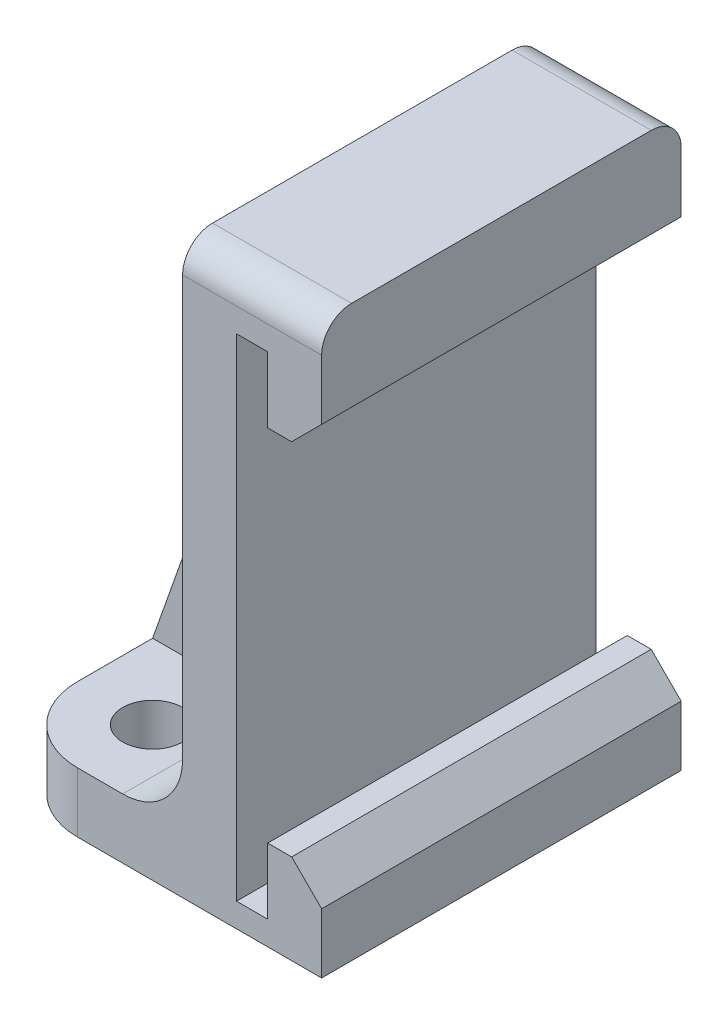
SolidWorks part; units mm, degrees
ref_plane "Front Plane" through (0, 0, 0) normal (0, 0, 1) x (1, 0, 0)
ref_plane "Top Plane" through (0, 0, 0) normal (0, 1, 0) x (1, 0, 0)
ref_plane "Right Plane" through (0, 0, 0) normal (1, 0, 0) x (0, 0, -1)
sketch "Sketch1" plane through (0, 0, 0) normal (0, 0, 1) x (1, 0, 0)
  line L0 (0, 0) -> (0, 25.4) construction
  line L1 (0, 25.4) -> (1.016, 25.4) construction
  line L2 (1.016, 25.4) -> (1.016, 0) construction
  line L3 (1.016, 0) -> (0, 0) construction
  line L4 (-0.3175, -0.3175) -> (-0.3175, 25.7175)
  line L5 (-0.3175, 25.7175) -> (1.3335, 25.7175)
  line L6 (1.3335, 25.7175) -> (1.3335, -0.3175) construction
  line L7 (1.3335, -0.3175) -> (-0.3175, -0.3175)
  line L8 (0.7937, 0) -> (0.7938, -1.5875) construction
  line L9 (1.016, 0) -> (4.191, 0) construction
  line L10 (4.191, -1.5875) -> (4.191, 0)
  line L11 (4.191, 0) -> (4.191, 3.175)
  line L12 (4.191, 3.175) -> (1.3335, 3.175)
  line L13 (1.016, 25.4) -> (1.016, 28.575) construction
  line L14 (1.016, 28.575) -> (4.191, 28.575)
  line L15 (4.191, 28.575) -> (4.191, 22.225)
  line L16 (4.191, 22.225) -> (1.3335, 22.225)
  line L17 (1.016, 28.575) -> (-3.175, 28.575)
  line L18 (-3.175, 28.575) -> (-3.175, -0.3175) construction
  line L20 (-3.175, -1.5875) -> (4.191, -1.5875)
  line L21 (-3.175, -1.5875) -> (-12.7, -1.5875)
  line L22 (-12.7, -1.5875) -> (-12.7, 1.5875)
  line L23 (-12.7, 1.5875) -> (-3.175, 1.5875)
  line L24 (1.3335, 25.7175) -> (1.3335, 22.225)
  line L25 (1.3335, 3.175) -> (1.3335, -0.3175)
  line L26 (-3.175, 28.575) -> (-3.175, 1.5875)
extrude "Boss-Extrude1" add sketch "Sketch1" along normal mid plane 19.05
fillet "Fillet1" radius 3.175 1 edges at (-3.175, 1.5875, 0)
sketch "Sketch2" plane through (0, 0, 0) normal (0, 0, 1) x (1, 0, 0)
  line L0 (-3.175, 28.575) -> (-12.7, 1.5875)
  line L1 (-12.7, 1.5875) -> (-3.175, 1.5875)
  line L2 (-3.175, 1.5875) -> (-3.175, 28.575)
extrude "Boss-Extrude2" add sketch "Sketch2" along normal mid plane 3.175
sketch "Sketch3" plane through (0, 1.5875, 0) normal (0, 1, 0) x (1, 0, 0)
  line L0 (-8.7312, -9.525) -> (-8.7312, -5.5563) construction
  line L1 (-6.35, -9.525) -> (-12.7, -9.525) construction
  line L2 (-8.7313, 9.525) -> (-8.7312, 5.5563) construction
  line L4 (-12.7, 1.5875) -> (-12.7, 9.525) construction
  line L6 (-12.7, -9.525) -> (-12.7, -1.5875) construction
  circle A0 centre (-8.7312, -5.5563) radius 1.5875
  circle A1 centre (-8.7312, 5.5563) radius 1.5875
  dimension "D1" = 3.9688
  dimension "D2" = 3.9688
  dimension "D3" = 3.9688
extrude "Cut-Extrude1" cut sketch "Sketch3" against normal up to surface (3.175 mm away) up to face at (-4.2545, -1.5875, 0)
chamfer "Chamfer1" distance 1.5875 angle 45 2 edges at (4.191, 3.175, 0) (4.191, 22.225, 0)
fillet "Fillet2" radius 1.5875 2 edges at (0.508, 28.575, -9.525) (0.508, 28.575, 9.525)
fillet "Fillet3" radius 3.9624 2 edges at (-12.7, 0, 9.525) (-12.7, 0, -9.525)
